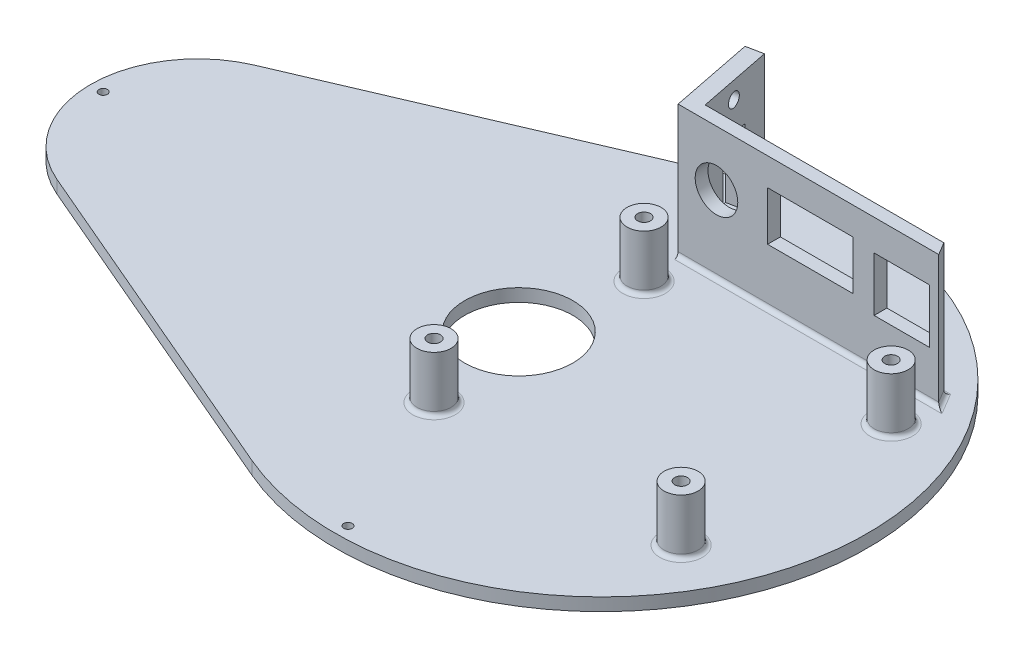
SolidWorks part; units mm, degrees
ref_plane "Front Plane" through (0, 0, 0) normal (0, 0, 1) x (1, 0, 0)
ref_plane "Top Plane" through (0, 0, 0) normal (0, 1, 0) x (1, 0, 0)
ref_plane "Right Plane" through (0, 0, 0) normal (1, 0, 0) x (0, 0, -1)
sketch "Sketch1" plane through (0, 0, 0) normal (0, 1, 0) x (1, 0, 0)
  line L0 (-104.6544, -23.1812) -> (-24.5987, -57.4557)
  line L1 (-104.6544, 23.1812) -> (-24.5987, 57.4557)
  arc A1 (-104.6544, 23.1812) -> (-104.6544, -23.1812) centre (-94.7298, 0) ccw
  arc A2 (-24.5987, -57.4557) -> (-24.5987, 57.4557) centre (0, 0) ccw
extrude "Boss-Extrude1" add sketch "Sketch1" along normal blind 3
sketch "Sketch2" plane through (0, 0, 0) normal (0, 1, 0) x (1, 0, 0)
  line L0 (0, 134.2014) -> (0, -142.3657) construction
  line L1 (-195.9442, 0) -> (170.0904, 0) construction
  circle A0 centre (-14.9937, -24.3042) radius 1.5
  circle A1 centre (-14.9937, -24.3042) radius 4
  circle A2 centre (43.0063, -24.3042) radius 1.5
  circle A3 centre (43.0063, -24.3042) radius 4
  circle A4 centre (-14.9937, 24.9958) radius 1.5
  circle A5 centre (-14.9937, 24.9958) radius 4
  circle A6 centre (43.0063, 24.9958) radius 1.5
  circle A7 centre (43.0063, 24.9958) radius 4
  dimension "D2" = 49.3
  dimension "D1" = 58
extrude "Boss-Extrude2" add sketch "Sketch2" along normal blind 16
sketch "Sketch3" plane through (0, 0, 0) normal (0, 1, 0) x (1, 0, 0)
  line L1 (-15.9933, 33.9958) -> (-19.8861, 53.5927)
  line L2 (-14.9933, 34.9958) -> (44.5747, 34.9958) construction
  line L3 (-16.0906, 54.3466) -> (-12.6439, 36.9958)
  line L4 (-12.6439, 36.9958) -> (43.3894, 36.9958)
  line L5 (43.3894, 36.9958) -> (45.1674, 33.9958)
  line L7 (-19.8861, 53.5927) -> (-16.0906, 54.3466)
  line L11 (-15.9933, 33.9958) -> (45.1674, 33.9958)
  line L14 (-18.7154, 34.9958) -> (54.5526, 34.9958) construction
  line L15 (-18.7154, 33.9958) -> (54.5526, 33.9958) construction
  dimension "D1" = 1
sketch "Sketch4" plane through (0, 0, 0) normal (0, 1, 0) x (1, 0, 0)
  line L0 (-94.1272, 0) -> (89.8409, 0) construction
  line L1 (0, 69.6103) -> (0, -72.0092) construction
  circle A0 centre (0, -45.0062) radius 5
extrude "Boss-Extrude4" add sketch "Sketch3" along normal blind 34
sketch "Sketch6" plane through (0, 0, -35.9958) normal (0, 0, -1) x (-1, 0, 0)
  line L0 (-58.6855, 16) -> (32.6323, 16) construction
  line L3 (-43.0063, 26.7419) -> (-30.0063, 26.7419)
  line L4 (-43.0063, 26.7419) -> (-43.0063, 14.0359)
  line L5 (-43.0063, 14.0359) -> (-30.0063, 14.0359)
  line L6 (-30.0063, 26.7419) -> (-30.0063, 14.0359)
  line L8 (-25.0063, 16) -> (-5.0063, 16)
  line L9 (-25.0063, 16) -> (-25.0063, 27.5)
  line L10 (-25.0063, 27.5) -> (-5.0063, 27.5)
  line L11 (-5.0063, 16) -> (-5.0063, 27.5)
  circle A0 centre (6.9937, 21) radius 5
  dimension "D8" = 5
  dimension "D2" = 13
  dimension "D5" = 5
  dimension "D6" = 20
  dimension "D7" = 11.5
  dimension "D9" = 12
extrude "Cut-Extrude1" cut sketch "Sketch6" against normal blind 5 and the other way blind 10
sketch "Sketch9" plane through (0, 3, 0) normal (0, 1, 0) x (1, 0, 0)
  line L0 (70.8168, 0) -> (-136.4647, 0) construction
  line L1 (-19.4029, 92.4565) -> (-19.4029, -97.4273) construction
  circle A0 centre (-19.4029, 0) radius 12.7
extrude "Cut-Extrude3" cut sketch "Sketch9" against normal blind 8
sketch "Sketch10" plane through (0, 3, 0) normal (0, 1, 0) x (1, 0, 0)
  line L0 (-23.4179, 54.6978) -> (-103.4737, 20.4233)
  line L1 (-103.4737, -20.4233) -> (-23.4179, -54.6978)
  line L2 (0, 69.6103) -> (0, -72.0092) construction
  arc A0 (-103.4737, 20.4233) -> (-103.4737, -20.4233) centre (-94.7298, 0) ccw
  arc A1 (-23.4179, -54.6978) -> (-23.4179, 54.6978) centre (0, 0) ccw
  circle A2 centre (-116.9461, 0) radius 1
  circle A3 centre (0, -59.5) radius 1
  circle A8 centre (0, 59.4895) radius 1
extrude "Cut-Extrude4" cut sketch "Sketch10" against normal blind 10 contours A2 | A3 | A8
fillet "Fillet1" radius 1 7 edges at (43.0063, 3, -20.9958) (-14.9937, 3, -20.9958) (-14.9937, 3, 28.3042) (43.0063, 3, 28.3042) (14.5871, 3, -33.9958) (44.2784, 3, -35.4958) (15.3727, 3, -36.9958)
sketch "Sketch11" plane through (-5.094, 0, 1.0119) normal (0.9808, 0, -0.1948) x (-0.1948, 0, -0.9808)
  line L1 (44.0755, 23.2089) -> (50.5755, 23.2089)
  line L2 (44.0755, 23.2089) -> (44.0755, 5.7089)
  line L3 (44.0755, 5.7089) -> (50.5755, 5.7089)
  line L4 (50.5755, 23.2089) -> (50.5755, 5.7089)
  circle A0 centre (47.3255, 29.9989) radius 1.62
  dimension "D1" = 17.5
  dimension "D2" = 6.5
extrude "Cut-Extrude5" cut sketch "Sketch11" against normal blind 10
